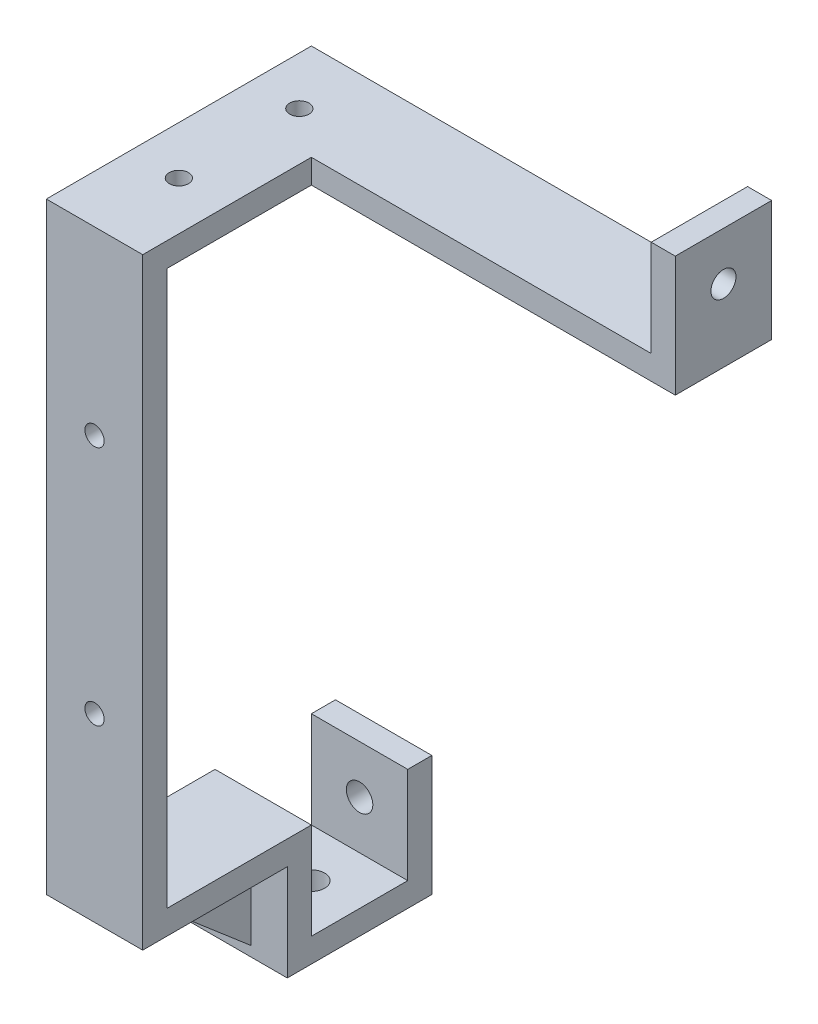
SolidWorks part; units mm, degrees
ref_plane "前视基准面" through (0, 0, 0) normal (0, 0, 1) x (1, 0, 0)
ref_plane "上视基准面" through (0, 0, 0) normal (0, 1, 0) x (1, 0, 0)
ref_plane "右视基准面" through (0, 0, 0) normal (1, 0, 0) x (0, 0, -1)
sketch "草图1" plane through (0, 0, 0) normal (0, 0, 1) x (1, 0, 0)
  line L1 (-9.8291, 14.8718) -> (10.1709, 14.8718)
  line L2 (-9.8291, 14.8718) -> (-9.8291, -130.1282)
  line L3 (-9.8291, -130.1282) -> (10.1709, -130.1282)
  line L4 (10.1709, 14.8718) -> (10.1709, -130.1282)
  dimension "D1" = 20
  dimension "D2" = 145
extrude "凸台-拉伸1" add sketch "草图1" against normal blind 5
sketch "草图2" plane through (0, 0, -5) normal (0, 0, -1) x (-1, 0, 0)
sketch "草图3" plane through (0, 0, -5) normal (0, 0, -1) x (-1, 0, 0)
  line L0 (-10.1709, 9.8718) -> (9.8291, 9.8718)
  line L1 (-10.1709, -130.1282) -> (-10.1709, 14.8718) construction
  line L2 (9.8291, 14.8718) -> (9.8291, -130.1282) construction
  line L3 (-10.1709, 14.8718) -> (9.8291, 14.8718) construction
  line L4 (-10.1709, 9.8718) -> (-10.1709, 14.8718)
  line L5 (-10.1709, 14.8718) -> (9.8291, 14.8718)
  line L6 (9.8291, 14.8718) -> (9.8291, 9.8718)
  dimension "D1" = 5
extrude "凸台-拉伸2" add sketch "草图3" along normal blind 50
sketch "草图4" plane through (0, 0, -5) normal (0, 0, -1) x (-1, 0, 0)
  line L0 (-10.1709, -105.1282) -> (9.8291, -105.1282)
  line L1 (-10.1709, -130.1282) -> (-10.1709, 9.8718) construction
  line L2 (9.8291, 9.8718) -> (9.8291, -130.1282) construction
  line L3 (-10.1709, 9.8718) -> (9.8291, 9.8718) construction
  line L4 (-10.1709, -110.1282) -> (9.8291, -110.1282)
  line L5 (-10.1709, -105.1282) -> (-10.1709, -110.1282)
  line L6 (9.8291, -110.1282) -> (9.8291, -105.1282)
  dimension "D1" = 115
  dimension "D2" = 5
extrude "凸台-拉伸3" add sketch "草图4" along normal blind 30
sketch "草图5" plane through (0, 0, -5) normal (0, 0, -1) x (-1, 0, 0)
  line L4 (9.8291, -110.1282) -> (-10.1709, -110.1282)
  line L5 (-10.1709, -110.1282) -> (-10.1709, -130.1282)
  line L6 (-10.1709, -130.1282) -> (9.8291, -130.1282)
  line L7 (9.8291, -130.1282) -> (9.8291, -110.1282)
  line L8 (9.8291, -110.1282) -> (-10.1709, -110.1282)
  line L9 (-10.1709, -110.1282) -> (-10.1709, -130.1282)
  line L10 (-10.1709, -130.1282) -> (9.8291, -130.1282)
  line L11 (9.8291, -130.1282) -> (9.8291, -110.1282)
  dimension "D1" = 0
extrude "切除-拉伸1" cut sketch "草图5" against normal blind 30
sketch "草图6" plane through (0, -110.1282, 0) normal (0, -1, 0) x (-1, 0, 0)
  line L0 (-10.1709, 30) -> (9.8291, 30)
  line L1 (-10.1709, 35) -> (-10.1709, 0) construction
  line L2 (9.8291, 35) -> (9.8291, 0) construction
  line L3 (-10.1709, 35) -> (9.8291, 35) construction
  line L4 (-10.1709, 30) -> (-10.1709, 35)
  line L5 (-10.1709, 35) -> (9.8291, 35)
  line L6 (9.8291, 35) -> (9.8291, 30)
  dimension "D1" = 5
extrude "凸台-拉伸4" add sketch "草图6" along normal blind 20
sketch "草图7" plane through (0, 0, -35) normal (0, 0, -1) x (-1, 0, 0)
  line L0 (9.8291, -125.1282) -> (-10.1709, -125.1282)
  line L1 (9.8291, -130.1282) -> (9.8291, -105.1282) construction
  line L2 (-10.1709, -105.1282) -> (-10.1709, -130.1282) construction
  line L3 (9.8291, -130.1282) -> (-10.1709, -130.1282) construction
  line L4 (9.8291, -125.1282) -> (9.8291, -130.1282)
  line L5 (9.8291, -130.1282) -> (-10.1709, -130.1282)
  line L6 (-10.1709, -130.1282) -> (-10.1709, -125.1282)
  dimension "D1" = 5
extrude "凸台-拉伸5" add sketch "草图7" along normal blind 20
ref_plane "基准面4" through (0.1709, 0, 0) normal (1, 0, 0) x (0, 0, -1)
sketch "草图9" plane through (0.1709, 0, 0) normal (1, 0, 0) x (0, 0, -1)
  line L0 (8.9653, -110.037) -> (29.9292, -127.9912)
  line L1 (29.9292, -127.9912) -> (29.9292, -110.037)
  line L2 (29.9292, -110.037) -> (8.9653, -110.037)
extrude "凸台-拉伸6" add sketch "草图9" along normal mid plane 5
sketch "草图10" plane through (0, 9.8718, 0) normal (0, -1, 0) x (1, 0, 0)
  circle A0 centre (0.1709, -17.5) radius 2
  circle A1 centre (0.1709, -42.5) radius 2
  dimension "D2" = 4
  dimension "D4" = 4
extrude "切除-拉伸2" cut sketch "草图10" against normal blind 5
sketch "草图11" plane through (0, 0, -5) normal (0, 0, -1) x (-1, 0, 0)
  circle A0 centre (-0.1709, -22.6282) radius 2
  circle A1 centre (-0.1709, -72.6282) radius 2
  dimension "D3" = 4
  dimension "D4" = 4
extrude "切除-拉伸3" cut sketch "草图11" against normal blind 5
sketch "草图12" plane through (0, -125.1282, 0) normal (0, 1, 0) x (1, 0, 0)
  circle A0 centre (0.1709, 45) radius 2.75
  dimension "D1" = 5.5
extrude "切除-拉伸4" cut sketch "草图12" against normal blind 5
sketch "草图13" plane through (0, 0, -55) normal (0, 0, -1) x (-1, 0, 0)
  line L4 (9.8291, -130.1282) -> (9.8291, -125.1282)
  line L5 (9.8291, -125.1282) -> (-10.1709, -125.1282)
  line L6 (-10.1709, -125.1282) -> (-10.1709, -130.1282)
  line L7 (-10.1709, -130.1282) -> (9.8291, -130.1282)
  line L8 (9.8291, -130.1282) -> (9.8291, -125.1282)
  line L9 (9.8291, -125.1282) -> (-10.1709, -125.1282)
  line L10 (-10.1709, -125.1282) -> (-10.1709, -130.1282)
  line L11 (-10.1709, -130.1282) -> (9.8291, -130.1282)
  dimension "D1" = 0
extrude "凸台-拉伸7" add sketch "草图13" along normal blind 5
sketch "草图14" plane through (0, -125.1282, 0) normal (0, 1, 0) x (1, 0, 0)
  line L0 (10.1709, 55) -> (-9.8291, 55)
  line L1 (10.1709, 60) -> (10.1709, 35) construction
  line L2 (-9.8291, 60) -> (-9.8291, 35) construction
  line L3 (-9.8291, 60) -> (10.1709, 60) construction
  line L4 (10.1709, 55) -> (10.1709, 60)
  line L5 (10.1709, 60) -> (-9.8291, 60)
  line L6 (-9.8291, 60) -> (-9.8291, 55)
  dimension "D1" = 5
extrude "凸台-拉伸8" add sketch "草图14" along normal blind 20
sketch "草图15" plane through (0, 0, -55) normal (0, 0, 1) x (1, 0, 0)
  circle A0 centre (0.1709, -115.1282) radius 2.75
  point P0 (0, 0)
  dimension "D1" = 5.5
extrude "切除-拉伸5" cut sketch "草图15" against normal blind 20
sketch "草图16" plane through (10.1709, 0, 0) normal (1, 0, 0) x (0, 0, -1)
  line L0 (35, 14.8718) -> (35, 9.8718)
  line L1 (55, 14.8718) -> (0, 14.8718) construction
  line L2 (55, 9.8718) -> (5, 9.8718) construction
  line L3 (55, 14.8718) -> (55, 9.8718) construction
  line L4 (35, 14.8718) -> (55, 14.8718)
  line L5 (55, 14.8718) -> (55, 9.8718)
  line L6 (55, 9.8718) -> (35, 9.8718)
  dimension "D1" = 20
extrude "凸台-拉伸9" add sketch "草图16" along normal blind 75.52
sketch "草图17" plane through (0, 14.8718, 0) normal (0, 1, 0) x (1, 0, 0)
  line L0 (80.6909, 55) -> (80.6909, 35)
  line L1 (-9.8291, 55) -> (85.6909, 55) construction
  line L2 (85.6909, 35) -> (10.1709, 35) construction
  line L3 (85.6909, 55) -> (85.6909, 35) construction
  line L4 (80.6909, 55) -> (85.6909, 55)
  line L5 (85.6909, 55) -> (85.6909, 35)
  line L6 (85.6909, 35) -> (80.6909, 35)
  dimension "D1" = 5
extrude "凸台-拉伸10" add sketch "草图17" along normal blind 20
sketch "草图18" plane through (80.6909, 0, 0) normal (-1, 0, 0) x (0, 0, 1)
  circle A0 centre (-45, 24.8718) radius 2.6
  dimension "D1" = 5.2
extrude "切除-拉伸6" cut sketch "草图18" against normal blind 20
